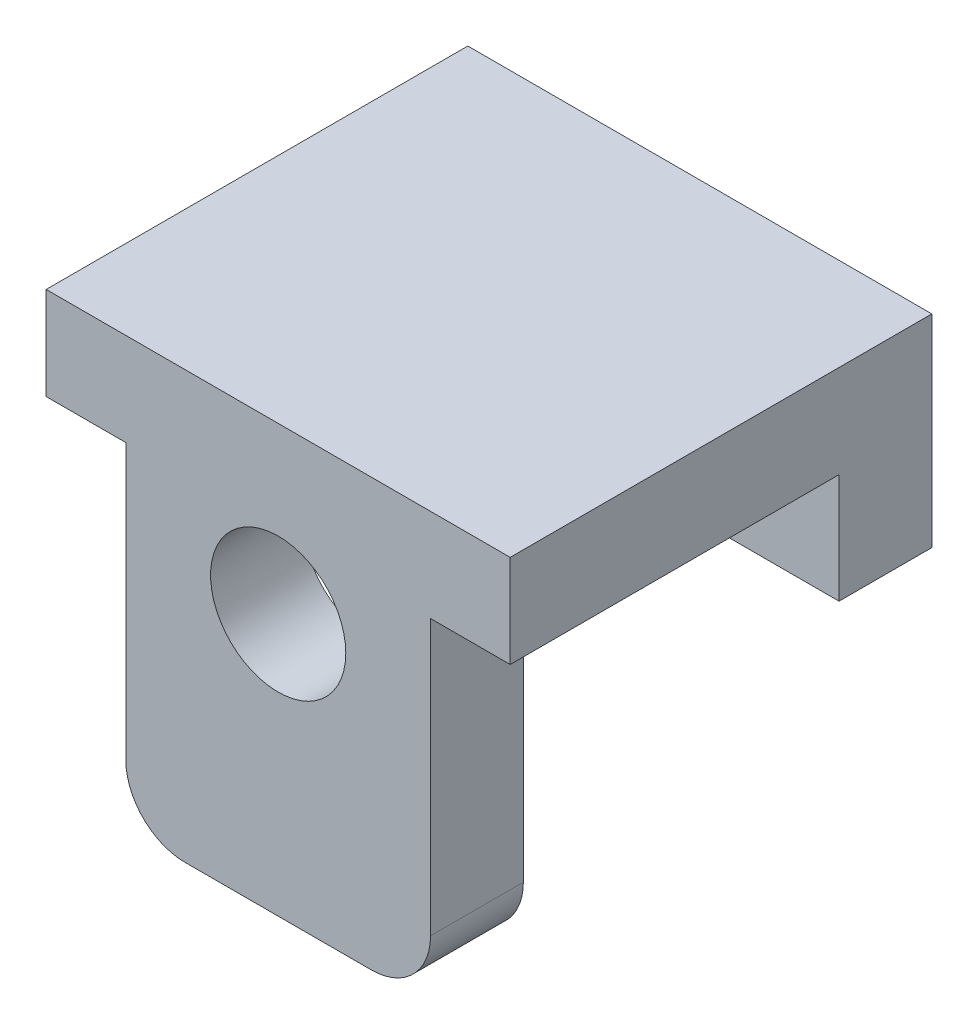
SolidWorks part; units mm, degrees
ref_plane "Front Plane" through (0, 0, 0) normal (0, 0, 1) x (1, 0, 0)
ref_plane "Top Plane" through (0, 0, 0) normal (0, 1, 0) x (1, 0, 0)
ref_plane "Right Plane" through (0, 0, 0) normal (1, 0, 0) x (0, 0, -1)
sketch "Sketch1" plane through (0, 0, 0) normal (0, 0, 1) x (1, 0, 0)
  line L0 (0, 14.8293) -> (0, -9.0084) construction
  line L1 (-13.0276, 0) -> (19.1256, 0) construction
  line L3 (-3.175, 1.385) -> (3.175, 1.385)
  line L4 (-3.175, 1.385) -> (-3.175, -1.385)
  line L5 (-3.175, -1.385) -> (3.175, -1.385)
  line L6 (3.175, 1.385) -> (3.175, -1.385)
  dimension "D1" = 6.35
  dimension "D2" = 2.77
extrude "Extrude1" add sketch "Sketch1" along normal blind 1.27
sketch "Sketch2" plane through (0, 0, 1.27) normal (0, 0, 1) x (1, 0, 0)
  line L0 (3.175, -1.385) -> (3.175, 1.385) construction
  line L1 (-3.175, 1.385) -> (3.175, 1.385)
  line L2 (-3.175, 1.385) -> (-3.175, 0.115)
  line L3 (-3.175, 0.115) -> (3.175, 0.115)
  line L4 (3.175, 1.385) -> (3.175, 0.115)
  dimension "D1" = 1.27
extrude "Extrude2" add sketch "Sketch2" along normal blind 4.5
sketch "Sketch3" plane through (0, 0, 5.77) normal (0, 0, 1) x (1, 0, 0)
  line L0 (0, 1.7604) -> (0, -1.8234) construction
  line L1 (-3.175, 0.115) -> (3.175, 0.115) construction
  line L2 (-2.085, 0.115) -> (2.085, 0.115)
  line L3 (-2.085, 0.115) -> (-2.085, -4.455)
  line L4 (-2.085, -4.455) -> (2.085, -4.455)
  line L5 (2.085, 0.115) -> (2.085, -4.455)
  line L6 (3.175, 1.385) -> (-3.175, 1.385) construction
  circle A0 centre (0, -0.875) radius 0.925
  dimension "D3" = 1.85
  dimension "D1" = 4.17
  dimension "D2" = 4.57
  dimension "D4" = 2.26
extrude "Extrude3" add sketch "Sketch3" against normal blind 1.27
fillet "Fillet1" radius 0.81 2 edges at (2.085, -4.455, 5.135) (-2.085, -4.455, 5.135)
